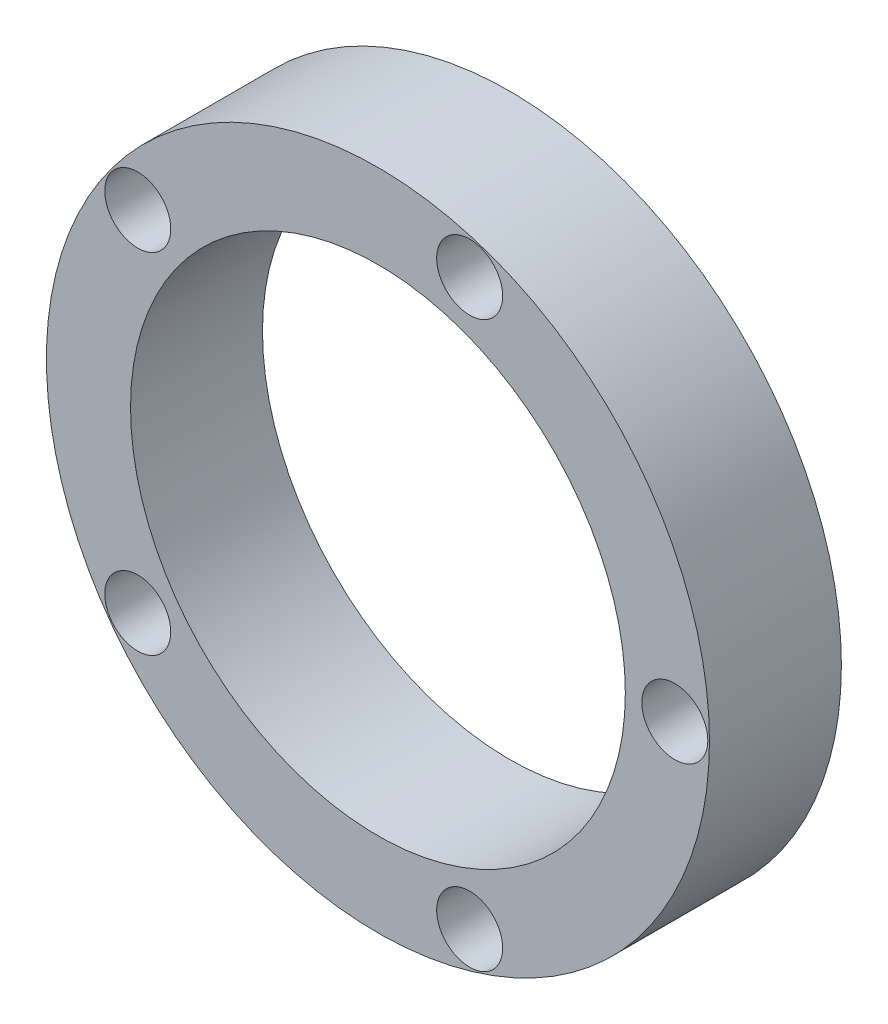
SolidWorks part; units mm, degrees
ref_plane "前视基准面" through (0, 0, 0) normal (0, 0, 1) x (1, 0, 0)
ref_plane "上视基准面" through (0, 0, 0) normal (0, 1, 0) x (1, 0, 0)
ref_plane "右视基准面" through (0, 0, 0) normal (1, 0, 0) x (0, 0, -1)
sketch "草图1" plane through (0, 0, 0) normal (0, 0, 1) x (1, 0, 0)
  circle A0 centre (0, 0) radius 12
  circle A1 centre (9, 0) radius 1
  circle A2 centre (2.7812, -8.5595) radius 1
  circle A3 centre (-7.2812, -5.2901) radius 1
  circle A4 centre (-7.2812, 5.2901) radius 1
  circle A5 centre (2.7812, 8.5595) radius 1
  point P15 (0, 0)
  dimension "D1" = 5
extrude "凸台-拉伸1" add sketch "草图1" along normal blind 2
sketch "草图3" plane through (0, 0, 2) normal (0, 0, 1) x (1, 0, 0)
  circle A0 centre (2.7812, -8.5595) radius 1 construction
  circle A1 centre (9, 0) radius 1
  circle A2 centre (9, 0) radius 1
  circle A3 centre (-7.2812, -5.2901) radius 1 construction
  circle A4 centre (-7.2812, 5.2901) radius 1 construction
  circle A5 centre (2.7812, 8.5595) radius 1 construction
  circle A6 centre (2.7812, -8.5595) radius 1
  circle A7 centre (-7.2812, -5.2901) radius 1
  circle A8 centre (-7.2812, 5.2901) radius 1
  circle A9 centre (2.7812, 8.5595) radius 1
  dimension "D1" = 0
extrude "凸台-拉伸2" add sketch "草图3" against normal blind 12
sketch "草图4" plane through (0, 0, 0) normal (0, 0, -1) x (-1, 0, 0)
  circle A0 centre (0, 0) radius 7
extrude "切除-拉伸1" cut sketch "草图4" against normal blind 12
sketch "草图6" plane through (0, 0, 0) normal (0, 0, -1) x (-1, 0, 0)
  circle A2 centre (0, 0) radius 11.5
  circle A3 centre (0, 0) radius 12 construction
  circle A4 centre (0, 0) radius 12
extrude "切除-拉伸2" cut sketch "草图6" against normal blind 4
sketch "草图8" plane through (0, 0, 2) normal (0, 0, 1) x (1, 0, 0)
  circle A0 centre (0, 0) radius 11.5
  circle A1 centre (0, 0) radius 7
extrude "凸台-拉伸4" add sketch "草图8" along normal blind 2
sketch "草图9" plane through (0, 0, 0) normal (0, 0, -1) x (-1, 0, 0)
  circle A0 centre (0, 0) radius 7.5
extrude "切除-拉伸3" cut sketch "草图9" against normal up to surface (4 mm away) up to face at (11.5, 0, 4)
sketch "草图12" plane through (0, 0, -10) normal (0, 0, -1) x (-1, 0, 0)
  circle A0 centre (-2.7812, -8.5595) radius 1 construction
  circle A1 centre (7.2812, 5.2901) radius 1 construction
  circle A2 centre (-2.7812, 8.5595) radius 1 construction
  circle A3 centre (-9, 0) radius 1 construction
  circle A4 centre (7.2812, -5.2901) radius 1 construction
  circle A5 centre (-2.7812, -8.5595) radius 1
  circle A6 centre (7.2812, 5.2901) radius 1
  circle A7 centre (-2.7812, 8.5595) radius 1
  circle A8 centre (-9, 0) radius 1
  circle A9 centre (7.2812, -5.2901) radius 1
extrude "切除-拉伸4" cut sketch "草图12" against normal blind 20
sketch "草图13" plane through (0, 0, 4) normal (0, 0, 1) x (1, 0, 0)
  circle A0 centre (0, 0) radius 10.05
  circle A1 centre (0, 0) radius 11.5 construction
  circle A2 centre (0, 0) radius 11.5
extrude "切除-拉伸5" cut sketch "草图13" against normal blind 10
